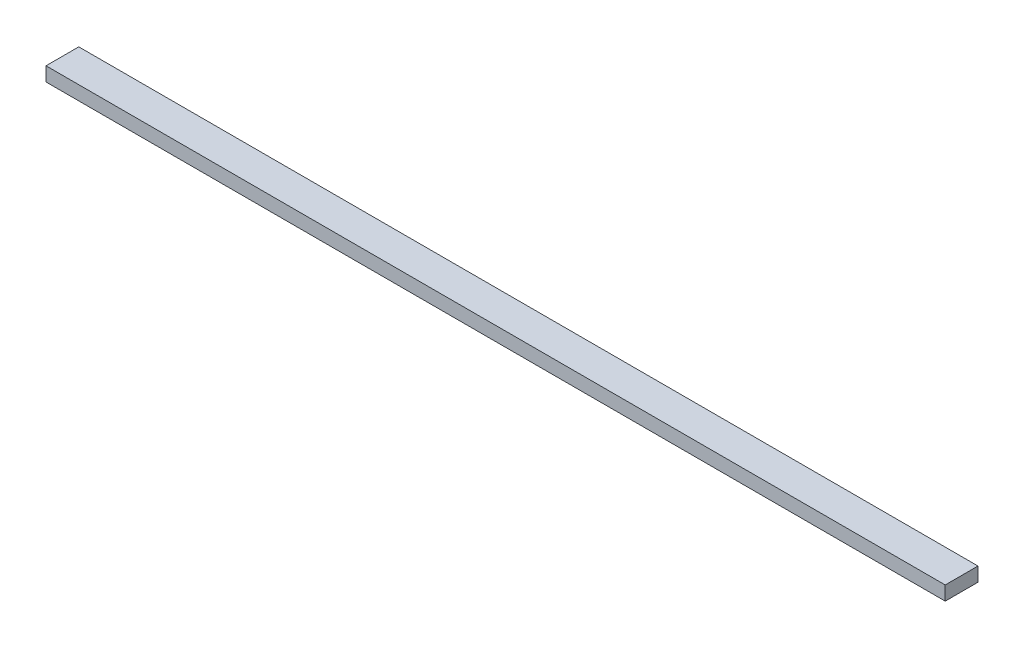
SolidWorks part; units mm, degrees
ref_plane "Front Plane" through (0, 0, 0) normal (0, 0, 1) x (1, 0, 0)
ref_plane "Top Plane" through (0, 0, 0) normal (0, 1, 0) x (1, 0, 0)
ref_plane "Right Plane" through (0, 0, 0) normal (1, 0, 0) x (0, 0, -1)
sketch "Sketch1" plane through (0, 0, 0) normal (0, 0, 1) x (1, 0, 0)
  line L0 (0, 0) -> (-2438.4, 0)
  line L1 (-2438.4, 0) -> (-2438.4, -38.1)
  line L2 (-2438.4, -38.1) -> (0, -38.1)
  line L3 (0, -38.1) -> (0, 0)
  dimension "D1" = 2438.4
  dimension "D2" = 38.1
extrude "Boss-Extrude1" add sketch "Sketch1" along normal blind 88.9 contours L0 L1 L2 L3
